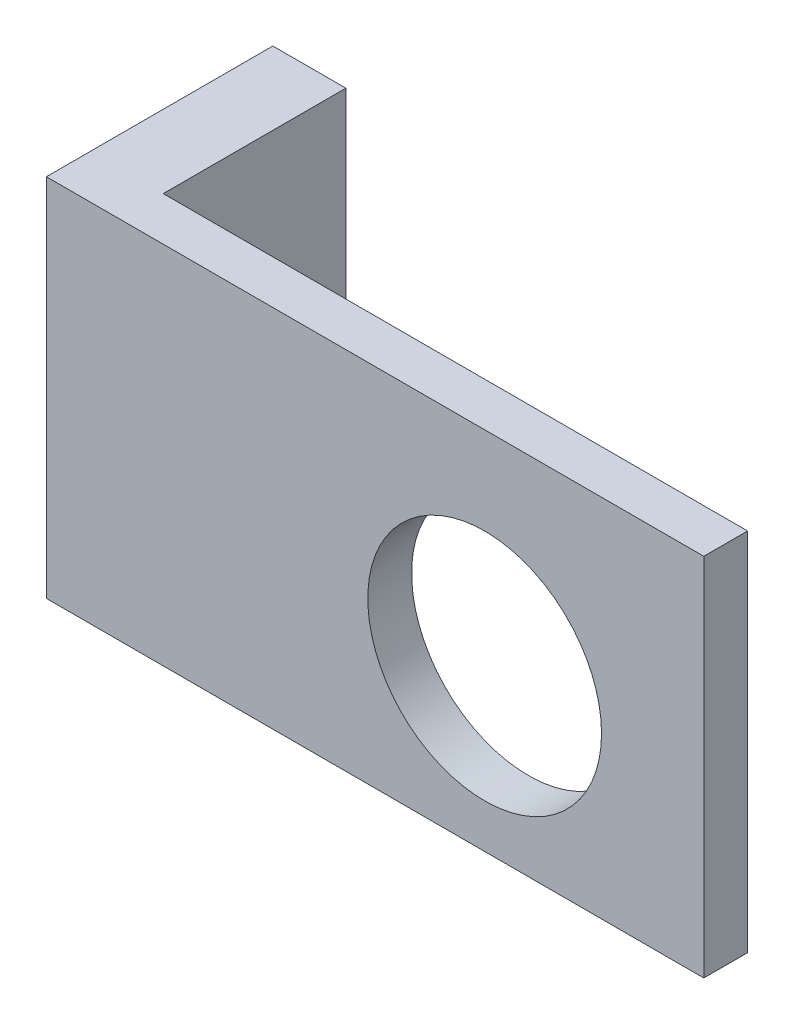
SolidWorks part; units mm, degrees
ref_plane "Front Plane" through (0, 0, 0) normal (0, 0, 1) x (1, 0, 0)
ref_plane "Top Plane" through (0, 0, 0) normal (0, 1, 0) x (1, 0, 0)
ref_plane "Right Plane" through (0, 0, 0) normal (1, 0, 0) x (0, 0, -1)
sketch "Sketch1" plane through (0, 0, 0) normal (0, 0, 1) x (1, 0, 0)
  line L1 (0, 0) -> (90, 0)
  line L2 (0, 0) -> (0, 50)
  line L3 (0, 50) -> (90, 50)
  line L4 (90, 0) -> (90, 50)
  circle A0 centre (60, 22) radius 16
  dimension "D3" = 32
  dimension "D1" = 50
  dimension "D2" = 90
  dimension "D4" = 60
  dimension "D5" = 28
extrude "Boss-Extrude1" add sketch "Sketch1" along normal blind 6
sketch "Sketch3" plane through (0, 0, 0) normal (0, 0, -1) x (-1, 0, 0)
  line L0 (0, 0) -> (-90, 0) construction
  line L1 (0, 50) -> (-10, 50)
  line L2 (0, 50) -> (0, 0)
  line L3 (0, 0) -> (-10, 0)
  line L4 (-10, 50) -> (-10, 0)
  dimension "D1" = 10
extrude "Boss-Extrude2" add sketch "Sketch3" along normal blind 25
scale "Scale1" scale about centroid uniform scaling yes scale factor 7.5
